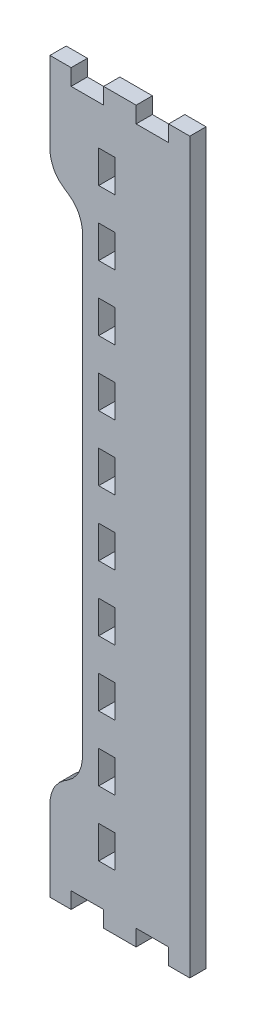
SolidWorks part; units mm, degrees
material "Acrylic (Medium-high impact)"
ref_plane "Front Plane" through (0, 0, 0) normal (0, 0, 1) x (1, 0, 0)
ref_plane "Top Plane" through (0, 0, 0) normal (0, 1, 0) x (1, 0, 0)
ref_plane "Right Plane" through (0, 0, 0) normal (1, 0, 0) x (0, 0, -1)
sketch "Model" plane through (0, 0, 0) normal (0, 0, 1) x (1, 0, 0)
  line L516 (803.2598, 23.2006) -> (810.7121, 23.2006)
  line L517 (810.7121, 23.2006) -> (810.7121, 28.9154)
  line L518 (810.7121, 28.9154) -> (822.1421, 28.9154)
  line L519 (822.1421, 28.9154) -> (822.1421, 23.2006)
  line L520 (822.1421, 23.2006) -> (833.5721, 23.2006)
  line L521 (833.5721, 23.2006) -> (833.5721, 28.9154)
  line L522 (833.5721, 28.9154) -> (845.0021, 28.9154)
  line L523 (845.0021, 28.9154) -> (845.0021, 23.2006)
  line L524 (845.0021, 23.2006) -> (852.4494, 23.2006)
  line L525 (852.4494, 23.2006) -> (852.4494, 279.6311)
  line L526 (852.4494, 279.6311) -> (845.0021, 279.6311)
  line L527 (845.0021, 279.6311) -> (845.0021, 273.9161)
  line L528 (845.0021, 273.9161) -> (833.5721, 273.9161)
  line L529 (833.5721, 273.9161) -> (833.5721, 279.6311)
  line L530 (833.5721, 279.6311) -> (822.1421, 279.6311)
  line L531 (822.1421, 279.6311) -> (822.1421, 273.9161)
  line L532 (822.1421, 273.9161) -> (810.7121, 273.9161)
  line L533 (810.7121, 273.9161) -> (810.7121, 279.6311)
  line L534 (810.7121, 279.6311) -> (803.2598, 279.6311)
  line L535 (803.2598, 279.6311) -> (803.2598, 251.0551)
  line L536 (803.2598, 251.0551) -> (803.2598, 250.3167)
  line L537 (803.2598, 250.3167) -> (803.6535, 248.0981)
  line L538 (803.6535, 248.0981) -> (804.5425, 245.776)
  line L539 (804.5425, 245.776) -> (804.7914, 245.3404)
  line L540 (804.7914, 245.3404) -> (805.0454, 244.9065)
  line L541 (805.0454, 244.9065) -> (806.6075, 242.9744)
  line L542 (806.6075, 242.9744) -> (808.543, 241.4077)
  line L543 (808.543, 241.4077) -> (808.9748, 241.1567)
  line L544 (808.9748, 241.1567) -> (809.4091, 240.906)
  line L545 (809.4091, 240.906) -> (811.342, 239.3404)
  line L546 (811.342, 239.3404) -> (812.9092, 237.4085)
  line L547 (812.9092, 237.4085) -> (813.1607, 236.9729)
  line L548 (813.1607, 236.9729) -> (813.4096, 236.539)
  line L549 (813.4096, 236.539) -> (814.3037, 234.217)
  line L550 (814.3037, 234.217) -> (814.6948, 231.9983)
  line L551 (814.6948, 231.9983) -> (814.6948, 231.2581)
  line L552 (814.6948, 231.2581) -> (814.6948, 71.5726)
  line L553 (814.6948, 71.5726) -> (814.6898, 71.071)
  line L554 (814.6898, 71.071) -> (814.3037, 68.6153)
  line L555 (814.3037, 68.6153) -> (813.4096, 66.2932)
  line L556 (813.4096, 66.2932) -> (813.1607, 65.8579)
  line L557 (813.1607, 65.8579) -> (812.9092, 65.4238)
  line L558 (812.9092, 65.4238) -> (811.342, 63.4919)
  line L559 (811.342, 63.4919) -> (809.4091, 61.9249)
  line L560 (809.4091, 61.9249) -> (808.9748, 61.674)
  line L561 (808.9748, 61.674) -> (808.543, 61.4233)
  line L562 (808.543, 61.4233) -> (806.6075, 59.8579)
  line L563 (806.6075, 59.8579) -> (805.0454, 57.9257)
  line L564 (805.0454, 57.9257) -> (804.7914, 57.4904)
  line L565 (804.7914, 57.4904) -> (804.5425, 57.0563)
  line L566 (804.5425, 57.0563) -> (803.6535, 54.7342)
  line L567 (803.6535, 54.7342) -> (803.2598, 52.5155)
  line L568 (803.2598, 52.5155) -> (803.2598, 51.7759)
  line L569 (803.2598, 51.7759) -> (803.2598, 23.2006)
  line L570 (820.4098, 254.2845) -> (820.4098, 259.9995)
  line L571 (820.4098, 259.9995) -> (826.1248, 259.9995)
  line L572 (826.1248, 259.9995) -> (826.1248, 248.5705)
  line L573 (826.1248, 248.5705) -> (820.4098, 248.5705)
  line L574 (820.4098, 248.5705) -> (820.4098, 254.2845)
  line L575 (820.4098, 231.425) -> (820.4098, 237.141)
  line L576 (820.4098, 237.141) -> (826.1248, 237.141)
  line L577 (826.1248, 237.141) -> (826.1248, 225.7105)
  line L578 (826.1248, 225.7105) -> (820.4098, 225.7105)
  line L579 (820.4098, 225.7105) -> (820.4098, 231.425)
  line L580 (820.4098, 208.566) -> (820.4098, 214.2807)
  line L581 (820.4098, 214.2807) -> (826.1248, 214.2807)
  line L582 (826.1248, 214.2807) -> (826.1248, 202.85)
  line L583 (826.1248, 202.85) -> (820.4098, 202.85)
  line L584 (820.4098, 202.85) -> (820.4098, 208.566)
  line L585 (820.4098, 185.7057) -> (820.4098, 191.4205)
  line L586 (820.4098, 191.4205) -> (826.1248, 191.4205)
  line L587 (826.1248, 191.4205) -> (826.1248, 179.991)
  line L588 (826.1248, 179.991) -> (820.4098, 179.991)
  line L589 (820.4098, 179.991) -> (820.4098, 185.7057)
  line L590 (820.4098, 162.8455) -> (820.4098, 168.5605)
  line L591 (820.4098, 168.5605) -> (826.1248, 168.5605)
  line L592 (826.1248, 168.5605) -> (826.1248, 157.1308)
  line L593 (826.1248, 157.1308) -> (820.4098, 157.1308)
  line L594 (820.4098, 157.1308) -> (820.4098, 162.8455)
  line L595 (820.4098, 139.9855) -> (820.4098, 145.7)
  line L596 (820.4098, 145.7) -> (826.1248, 145.7)
  line L597 (826.1248, 145.7) -> (826.1248, 134.2705)
  line L598 (826.1248, 134.2705) -> (820.4098, 134.2705)
  line L599 (820.4098, 134.2705) -> (820.4098, 139.9855)
  line L600 (820.4098, 117.125) -> (820.4098, 122.841)
  line L601 (820.4098, 122.841) -> (826.1248, 122.841)
  line L602 (826.1248, 122.841) -> (826.1248, 111.4105)
  line L603 (826.1248, 111.4105) -> (820.4098, 111.4105)
  line L604 (820.4098, 111.4105) -> (820.4098, 117.125)
  line L605 (820.4098, 94.266) -> (820.4098, 99.9807)
  line L606 (820.4098, 99.9807) -> (826.1248, 99.9807)
  line L607 (826.1248, 99.9807) -> (826.1248, 88.55)
  line L608 (826.1248, 88.55) -> (820.4098, 88.55)
  line L609 (820.4098, 88.55) -> (820.4098, 94.266)
  line L610 (820.4098, 71.4057) -> (820.4098, 77.1205)
  line L611 (820.4098, 77.1205) -> (826.1248, 77.1205)
  line L612 (826.1248, 77.1205) -> (826.1248, 65.691)
  line L613 (826.1248, 65.691) -> (820.4098, 65.691)
  line L614 (820.4098, 65.691) -> (820.4098, 71.4057)
  line L615 (820.4098, 48.5455) -> (820.4098, 54.2605)
  line L616 (820.4098, 54.2605) -> (826.1248, 54.2605)
  line L617 (826.1248, 54.2605) -> (826.1248, 42.8308)
  line L618 (826.1248, 42.8308) -> (820.4098, 42.8308)
  line L619 (820.4098, 42.8308) -> (820.4098, 48.5455)
extrude "Boss-Extrude1" add sketch "Model" along normal blind 5.715
